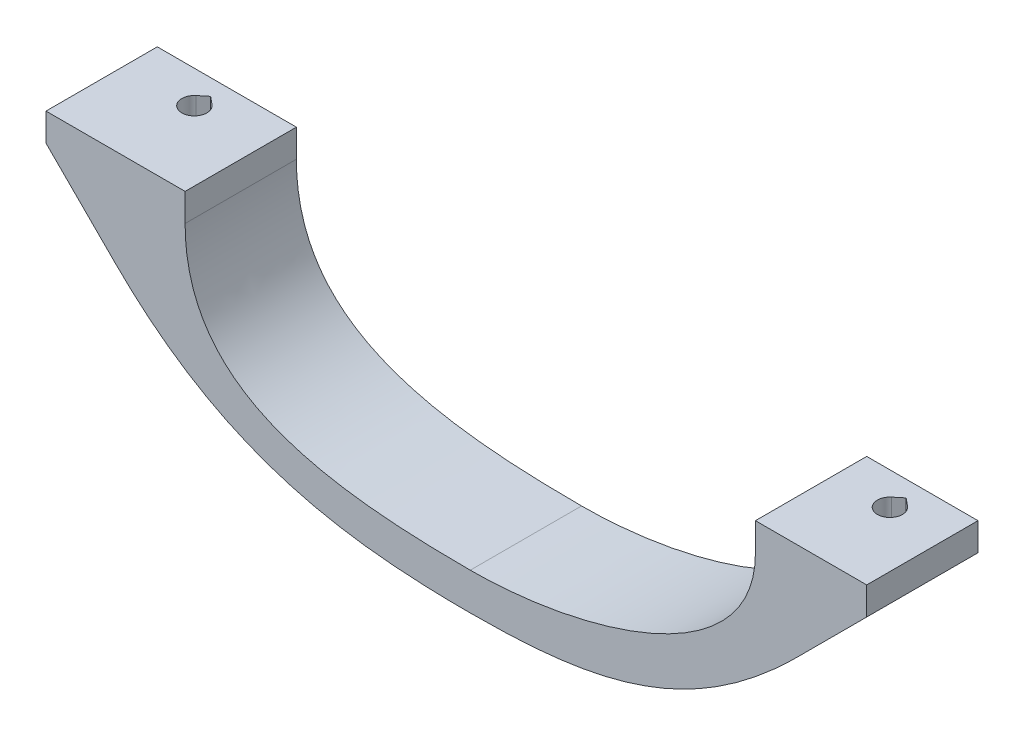
SolidWorks part; units mm, degrees
ref_plane "Front Plane" through (0, 0, 0) normal (0, 0, 1) x (1, 0, 0)
ref_plane "Top Plane" through (0, 0, 0) normal (0, 1, 0) x (1, 0, 0)
ref_plane "Right Plane" through (0, 0, 0) normal (1, 0, 0) x (0, 0, -1)
sketch "Sketch1" plane through (0, 0, 0) normal (0, 0, 1) x (1, 0, 0)
  line L0 (88.5, -40) -> (76.5, -40) construction
  line L1 (15, -40) -> (0, -40) construction
  line L2 (88.5, -40) -> (76.5, -40)
  line L3 (15, -40) -> (0, -40)
  line L4 (15, -40) -> (76.5, -40) construction
  line L5 (45.75, -40) -> (45.75, -60) construction
  line L6 (15, -40) -> (15, -43)
  line L7 (0, -40) -> (0, -43)
  line L8 (63.1923, -60) -> (28.3077, -60) construction
  line L9 (15, -59.2382) -> (15, -24.9064) construction
  line L10 (0, -43) -> (7.5, -50.5)
  line L11 (45.75, -60) -> (45.75, -64) construction
  line L12 (62.5753, -64) -> (28.9247, -64) construction
  line L13 (15.3084, -58.3084) -> (-3.2087, -39.7913) construction
  line L14 (88.5, -40) -> (88.5, -43)
  line L15 (76.5, -40) -> (76.5, -43)
  line L16 (30.6262, -60) -> (60.8738, -60) construction
  line L17 (76.5, -53.9076) -> (76.5, -27.2556) construction
  line L18 (88.5, -43) -> (81, -50.5)
  line L19 (29.8261, -64) -> (61.6739, -64) construction
  line L20 (72.261, -59.239) -> (90.3899, -41.1101) construction
  spline S0 degree 3 poles (15, -43) (15, -57.8895) (29.668, -60) (45.75, -60) knots 0 0 0 0 1 1 1 1
  spline S1 degree 3 poles (7.5, -50.5) (19.0732, -62.0732) (31.7289, -64) (45.75, -64) knots 0 0 0 0 1 1 1 1
  spline S2 degree 3 poles (76.5, -43) (76.5, -54.6616) (58.3532, -60) (45.75, -60) knots 0 0 0 0 1 1 1 1
  spline S3 degree 3 poles (81, -50.5) (69.4421, -62.0579) (59.0199, -64) (45.75, -64) knots 0 0 0 0 1 1 1 1
  dimension "D1" = 20
  dimension "D2" = 3
  dimension "D3" = 7.5
  dimension "D4" = 45
  dimension "D5" = 4
  dimension "D6" = 7.5
  dimension "D7" = 45
extrude "Boss-Extrude1" add sketch "Sketch1" against normal blind 12
sketch "Sketch2" plane through (0, -40, 0) normal (0, 1, 0) x (1, 0, 0)
  line L0 (0, 12) -> (15, 0) construction
  line L1 (76.5, 12) -> (88.5, 0) construction
  line L2 (82.5, 6) -> (82.5, 8.5) construction
  line L5 (7.5, 6) -> (7.5, 8.5) construction
  line L6 (7.5, 12) -> (7.5, 0) construction
  circle A0 centre (7.5, 6) radius 1.35 construction
  circle A1 centre (82.5, 6) radius 1.35 construction
  circle A2 centre (82.5, 8.5) radius 1.35
  circle A3 centre (7.5, 8.5) radius 1.35
  dimension "D1" = 2.7
  dimension "D2" = 2.5
extrude "Cut-Extrude1" cut sketch "Sketch2" against normal through all
ref_plane "Plane1" through (0, -80, 0) normal (0, 1, 0) x (1, 0, 0)
sketch "Sketch4" plane through (0, -80, 0) normal (0, 1, 0) x (1, 0, 0)
  circle A0 centre (7.5, 8.5) radius 2.5
  circle A1 centre (82.5, 8.5) radius 2.5
  circle A2 centre (82.5, 8.5) radius 1.35 construction
  dimension "D1" = 5
extrude "Cut-Extrude3" cut sketch "Sketch4" along normal offset from surface (37 mm away) 3 up to face at (7.5, -40, -7.15)
sketch "Sketch7" plane through (0, -40, 0) normal (0, 1, 0) x (1, 0, 0)
  line L2 (7.5, 9.85) -> (7.5, 10.25) construction
  line L5 (7.5, 10.25) -> (8.359, 9.5414)
  line L6 (7.5, 10.25) -> (6.641, 9.5414)
  arc A2 (8.359, 9.5414) -> (6.641, 9.5414) centre (7.5, 8.5) ccw
  circle A13 centre (7.5, 8.5) radius 1.35 construction
  dimension "D1" = 0.4
extrude "Cut-Extrude4" cut sketch "Sketch7" against normal through all
sketch "Sketch8" plane through (0, -40, 0) normal (0, 1, 0) x (1, 0, 0)
  line L0 (82.5, 9.85) -> (82.5, 10.25) construction
  line L1 (82.5, 10.25) -> (83.359, 9.5414)
  line L2 (82.5, 10.25) -> (81.641, 9.5414)
  circle A0 centre (82.5, 8.5) radius 1.35 construction
  arc A1 (83.359, 9.5414) -> (81.641, 9.5414) centre (82.5, 8.5) ccw
  point P7 (83.4861, 9.422)
  point P8 (0, 0)
  dimension "D1" = 0.4
extrude "Cut-Extrude5" cut sketch "Sketch8" against normal through all
